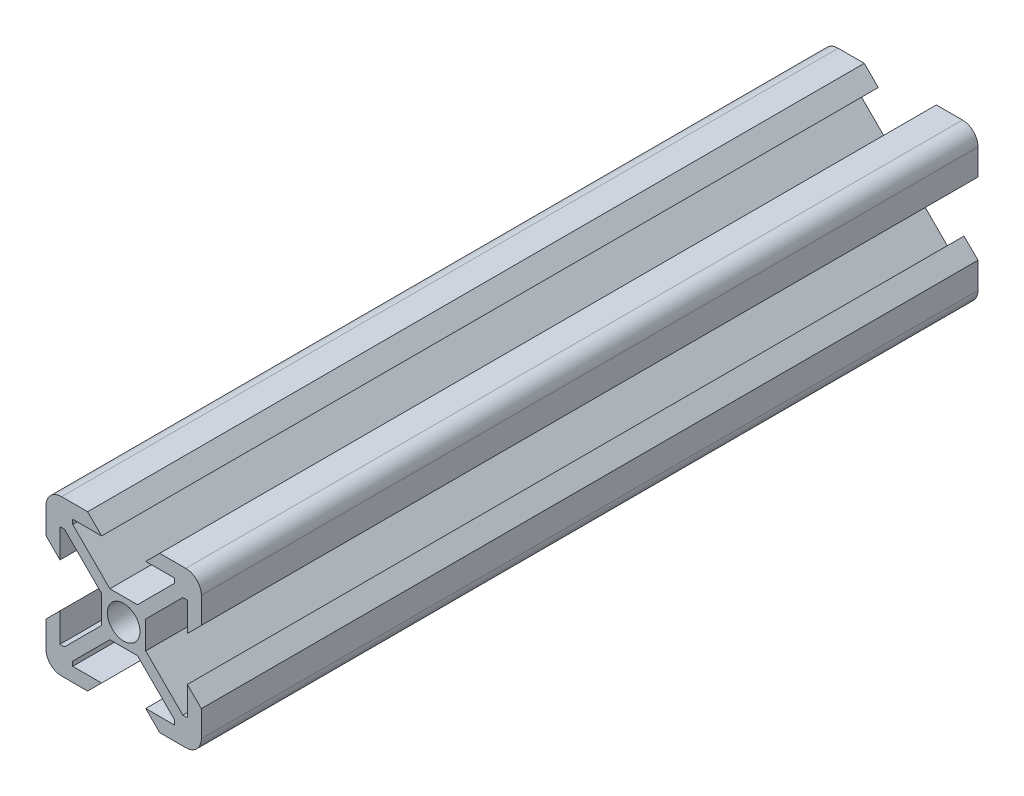
SolidWorks part; units mm, degrees
ref_plane "Front Plane" through (0, 0, 0) normal (0, 0, 1) x (1, 0, 0)
ref_plane "Top Plane" through (0, 0, 0) normal (0, 1, 0) x (1, 0, 0)
ref_plane "Right Plane" through (0, 0, 0) normal (1, 0, 0) x (0, 0, -1)
sketch "Sketch1" plane through (0, 0, 0) normal (0, 0, 1) x (1, 0, 0)
  line L0 (0, 10) -> (0, -2.84) construction
  line L1 (8, 10) -> (4.64, 10)
  line L2 (10, 4.64) -> (8.2, 2.84)
  line L3 (8.2, 2.84) -> (8.2, 6.56)
  line L4 (8.2, 6.56) -> (6.56, 6.56)
  line L5 (6.56, 6.56) -> (2.84, 2.84)
  line L6 (10, 4.64) -> (10, 8)
  line L7 (2.84, -2.84) -> (-2.84, -2.84)
  line L8 (2.84, -2.84) -> (2.84, 2.84)
  line L9 (2.84, 2.84) -> (-2.84, 2.84)
  line L10 (-2.84, -2.84) -> (-2.84, 2.84)
  line L11 (2.84, -2.84) -> (-2.84, 2.84) construction
  line L12 (2.84, 2.84) -> (-2.84, -2.84) construction
  line L13 (-4.64, 10) -> (-2.84, 8.2)
  line L14 (-2.84, 8.2) -> (-6.56, 8.2)
  line L15 (-6.56, 8.2) -> (-6.56, 6.56)
  line L16 (-6.56, 6.56) -> (-2.84, 2.84)
  line L17 (6.56, 6.56) -> (2.84, 2.84)
  line L18 (6.56, 8.2) -> (6.56, 6.56)
  line L19 (2.84, 8.2) -> (6.56, 8.2)
  line L20 (4.64, 10) -> (2.84, 8.2)
  line L21 (-4.64, 10) -> (-8, 10)
  line L22 (6.56, -6.56) -> (2.84, -2.84)
  line L23 (8.2, -6.56) -> (6.56, -6.56)
  line L24 (8.2, -2.84) -> (8.2, -6.56)
  line L25 (10, -4.64) -> (8.2, -2.84)
  line L26 (10, -8) -> (10, -4.64)
  line L27 (4.64, -10) -> (2.84, -8.2)
  line L28 (2.84, -8.2) -> (6.56, -8.2)
  line L29 (6.56, -8.2) -> (6.56, -6.56)
  line L30 (6.56, -6.56) -> (2.84, -2.84)
  line L31 (4.64, -10) -> (8, -10)
  line L32 (-6.56, -6.56) -> (-2.84, -2.84)
  line L33 (-6.56, -8.2) -> (-6.56, -6.56)
  line L34 (-2.84, -8.2) -> (-6.56, -8.2)
  line L35 (-4.64, -10) -> (-2.84, -8.2)
  line L36 (-8, -10) -> (-4.64, -10)
  line L37 (-10, -4.64) -> (-8.2, -2.84)
  line L38 (-8.2, -2.84) -> (-8.2, -6.56)
  line L39 (-8.2, -6.56) -> (-6.56, -6.56)
  line L40 (-6.56, -6.56) -> (-2.84, -2.84)
  line L41 (-10, -4.64) -> (-10, -8)
  line L42 (-6.56, 6.56) -> (-2.84, 2.84)
  line L43 (-8.2, 6.56) -> (-6.56, 6.56)
  line L44 (-8.2, 2.84) -> (-8.2, 6.56)
  line L45 (-10, 4.64) -> (-8.2, 2.84)
  line L46 (-10, 8) -> (-10, 4.64)
  line L47 (-7.6207, 6.56) -> (-2.84, 1.7793)
  line L48 (-6.56, 7.6207) -> (-1.7793, 2.84)
  line L49 (6.56, 7.6207) -> (1.7793, 2.84)
  line L50 (7.6207, 6.56) -> (2.84, 1.7793)
  line L51 (-2.84, 0) -> (2.84, 0) construction
  line L52 (7.6207, -6.56) -> (2.84, -1.7793)
  line L53 (6.56, -7.6207) -> (1.7793, -2.84)
  line L54 (-6.56, -7.6207) -> (-1.7793, -2.84)
  line L55 (-7.6207, -6.56) -> (-2.84, -1.7793)
  circle A0 centre (0, 0) radius 2.1
  arc A1 (-10, -8) -> (-8, -10) centre (-8, -8) ccw
  arc A2 (8, -10) -> (10, -8) centre (8, -8) ccw
  arc A3 (10, 8) -> (8, 10) centre (8, 8) ccw
  arc A4 (-10, 8) -> (-8, 10) centre (-8, 8) cw
  point P0 (0, 0)
  point P6 (0, 0)
  point P61 (0, 0)
  point P78 (-10, 10)
  dimension "D3" = 4.2
  dimension "D8" = 2
  dimension "D1" = 0.75
  dimension "D2" = 5.68
  dimension "D4" = 4
  dimension "D5" = 45
  dimension "D6" = 1.64
  dimension "D7" = 1.8
  dimension "D9" = 10
extrude "Boss-Extrude1" add sketch "Sketch1" along normal blind 100 contours L10 L7 L8 L9 A0 | A4 L46 L45 L44 L43 L15 L14 L13 L21 | L6 A3 L1 L20 L19 L18 L4 L3 L2 | L41 A1 L36 L35 L34 L33 L39 L38 L37 | L31 A2 L26 L25 L24 L23 L29 L28 L27 | L23 L52 L8 L22 | L53 L29 L22 L7 | L33 L54 L7 L32 | L55 L39 L32 L10 | L43 L47 L10 L16 | L48 L15 L16 L9 | L18 L49 L9 L5 | L50 L4 L5 L8
